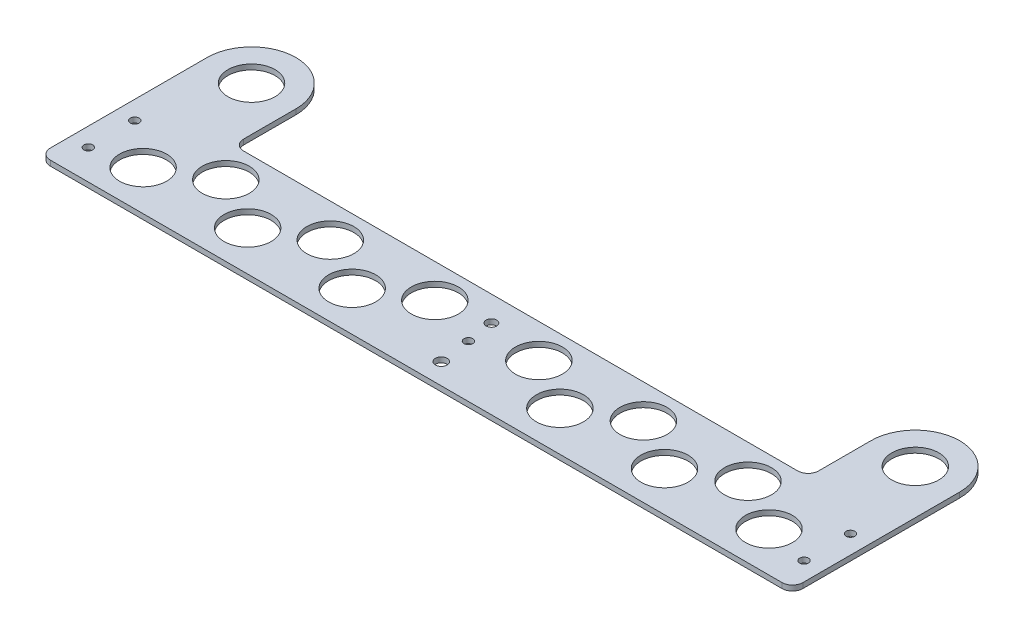
SolidWorks part; units mm, degrees
material "6063-T6"
ref_plane "Front" through (0, 0, 0) normal (0, 0, 1) x (1, 0, 0)
ref_plane "Top" through (0, 0, 0) normal (0, 1, 0) x (1, 0, 0)
ref_plane "Right" through (0, 0, 0) normal (1, 0, 0) x (0, 0, -1)
sketch "Sketch1" plane through (0, 0, 0) normal (0, 1, 0) x (1, 0, 0)
  line L0 (0, 0) -> (403.225, 0) construction
  line L5 (-26.9875, 0) -> (-26.9875, -95.25)
  line L6 (430.2125, 0) -> (430.2125, -95.25)
  line L7 (423.8625, -101.6) -> (-20.6375, -101.6)
  line L8 (26.9875, 0) -> (26.9875, -31.75)
  line L9 (376.2375, 0) -> (376.2375, -31.75)
  line L10 (369.8875, -38.1) -> (33.3375, -38.1)
  line L11 (403.225, 0) -> (403.225, 26.9875) construction
  circle A0 centre (0, 0) radius 14.2875
  circle A1 centre (403.225, 0) radius 14.2875
  arc A2 (26.9875, 0) -> (-26.9875, 0) centre (0, 0) ccw
  arc A3 (430.2125, 0) -> (376.2375, 0) centre (403.225, 0) ccw
  circle A4 centre (0, 0) radius 26.9875 construction
  circle A5 centre (403.225, 0) radius 26.9875 construction
  arc A6 (376.2375, -31.75) -> (369.8875, -38.1) centre (369.8875, -31.75) cw
  arc A7 (430.2125, -95.25) -> (423.8625, -101.6) centre (423.8625, -95.25) cw
  arc A8 (-26.9875, -95.25) -> (-20.6375, -101.6) centre (-20.6375, -95.25) ccw
  arc A9 (26.9875, -31.75) -> (33.3375, -38.1) centre (33.3375, -31.75) ccw
  point P24 (-26.9875, -101.6)
  point P27 (26.9875, -38.1)
  dimension "D3" = 28.575
  dimension "D5" = 28.575
  dimension "D7" = 6.35
  dimension "D9" = 128.5875
  dimension "D1" = 12.7
  dimension "D2" = 101.6
  dimension "D4" = 403.225
  dimension "D6" = 38.1
  dimension "D8" = 457.2
extrude "Boss-Extrude1" add sketch "Sketch1" along normal blind 3.175
sketch "Sketch2" plane through (0, 3.175, 0) normal (0, 1, 0) x (1, 0, 0)
  line L1 (-26.9875, 0) -> (-26.9875, -95.25) construction
  line L2 (-20.6375, -101.6) -> (423.8625, -101.6) construction
  line L3 (430.2125, -95.25) -> (430.2125, 0) construction
  circle A1 centre (204.1525, -88.9) radius 3.556
  circle A3 centre (199.0725, -53.34) radius 3.175
  dimension "D3" = 231.14
  dimension "D1" = 231.14
  dimension "D2" = 12.7
  dimension "D4" = 48.26
extrude "Cut-Extrude1" cut sketch "Sketch2" against normal up to next
sketch "Sketch3" plane through (0, 3.175, 0) normal (0, 1, 0) x (1, 0, 0)
  line L0 (201.6125, -38.1) -> (201.6125, 7.4644) construction
  line L1 (369.8875, -38.1) -> (33.3375, -38.1) construction
  circle A1 centre (-15.7797, -55.159) radius 2.667
  circle A2 centre (419.0047, -55.159) radius 2.667
  circle A3 centre (-15.7797, -83.3715) radius 2.667
  circle A4 centre (419.0047, -83.3715) radius 2.667
  dimension "D1" = 5.334
extrude "Cut-Extrude2" cut sketch "Sketch3" against normal up to next
sketch "Sketch4" plane through (0, 3.175, 0) normal (0, 1, 0) x (1, 0, 0)
  line L0 (201.6125, -38.1) -> (201.6125, -101.6) construction
  line L1 (369.8875, -38.1) -> (33.3375, -38.1) construction
  line L2 (-20.6375, -101.6) -> (423.8625, -101.6) construction
  circle A0 centre (201.6125, -69.85) radius 2.667
  dimension "D1" = 5.334
extrude "Cut-Extrude3" cut sketch "Sketch4" against normal up to next
sketch "Sketch5" plane through (0, 3.175, 0) normal (0, 1, 0) x (1, 0, 0)
  line L0 (430.2125, 0) -> (430.2125, 26.9875) construction
  line L1 (403.225, 26.9875) -> (430.2125, 26.9875) construction
  arc A0 (430.2125, 0) -> (376.2375, 0) centre (403.225, 0) ccw construction
sketch "Sketch6" plane through (0, 3.175, 0) normal (0, 1, 0) x (1, 0, 0)
  line L0 (201.6125, -101.6) -> (201.6125, -38.1) construction
  line L1 (-20.6375, -101.6) -> (423.8625, -101.6) construction
  line L2 (369.8875, -38.1) -> (33.3375, -38.1) construction
  circle A0 centre (11.5017, -77.3672) radius 14.2875
  circle A1 centre (43.0029, -58.636) radius 14.2875
  circle A2 centre (75.0017, -77.3672) radius 14.2875
  circle A3 centre (106.5029, -58.636) radius 14.2875
  circle A4 centre (138.5017, -77.3672) radius 14.2875
  circle A5 centre (170.0029, -58.636) radius 14.2875
  circle A12 centre (233.2221, -58.636) radius 14.2875
  circle A13 centre (264.7233, -77.3672) radius 14.2875
  circle A14 centre (296.7221, -58.636) radius 14.2875
  circle A15 centre (328.2233, -77.3672) radius 14.2875
  circle A16 centre (360.2221, -58.636) radius 14.2875
  circle A17 centre (391.7233, -77.3672) radius 14.2875
  point P30 (0, 0)
  point P31 (0, 0)
  point P32 (49.1038, -59.3579)
  point P33 (0, 0)
  dimension "D1" = 28.575
  dimension "D2" = 3
extrude "Cut-Extrude4" cut sketch "Sketch6" against normal up to next
